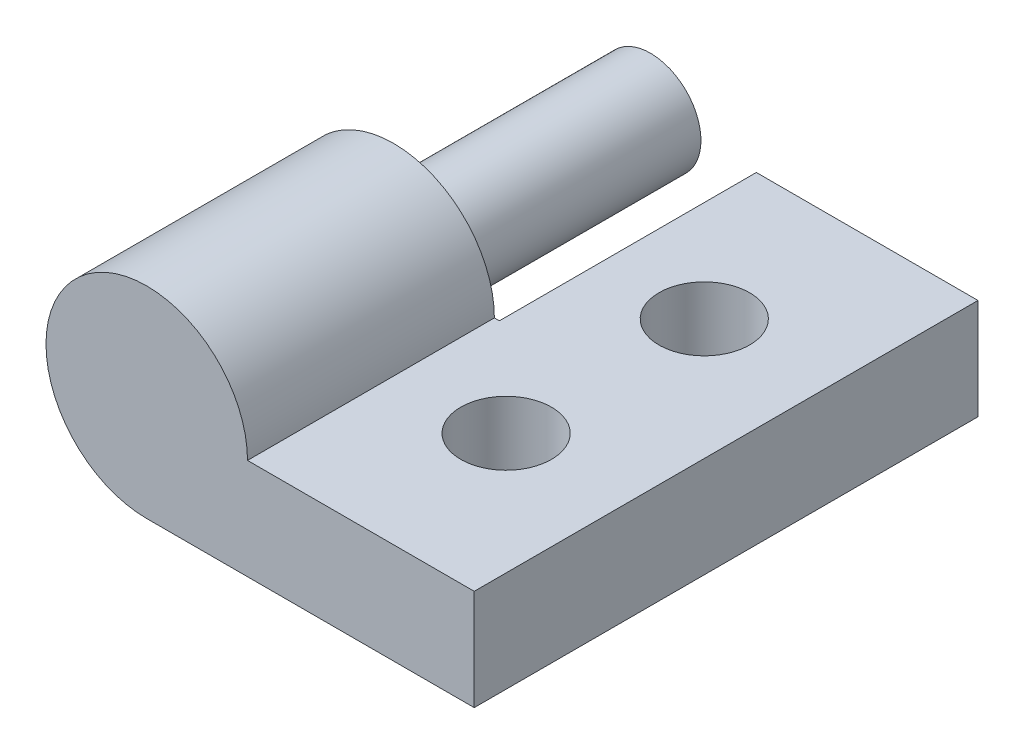
SolidWorks part; units mm, degrees
ref_plane "Front Plane" through (0, 0, 0) normal (0, 0, 1) x (1, 0, 0)
ref_plane "Top Plane" through (0, 0, 0) normal (0, 1, 0) x (1, 0, 0)
ref_plane "Right Plane" through (0, 0, 0) normal (1, 0, 0) x (0, 0, -1)
sketch "Sketch2" plane through (0, 0, 0) normal (0, 0, 1) x (1, 0, 0)
  line L1 (0, 0) -> (-16.51, 0)
  line L2 (0, 0) -> (0, 5.08)
  line L3 (0, 5.08) -> (-11.43, 5.08)
  arc A0 (-11.43, 5.08) -> (-16.51, 0) centre (-16.51, 5.08) ccw
  dimension "D3" = 5.08
  dimension "D1" = 16.51
  dimension "D2" = 5.08
extrude "Boss-Extrude1" add sketch "Sketch2" along normal blind 25.4
sketch "Sketch5" plane through (0, 5.08, 0) normal (0, 1, 0) x (1, 0, 0)
  line L0 (-6.096, -15.4093) -> (-6.096, -9.9907) construction
  line L1 (-6.096, -19.9813) -> (-6.096, -25.4) construction
  line L2 (0, -25.4) -> (-11.43, -25.4) construction
  line L3 (-6.096, -5.4187) -> (-6.096, 0) construction
  line L4 (0, 0) -> (-11.43, 0) construction
  line L5 (-6.096, -7.7047) -> (-16.51, -7.7047) construction
  line L9 (-16.51, -25.4) -> (-16.51, 0) construction
  circle A0 centre (-6.096, -17.6953) radius 2.286
  circle A1 centre (-6.096, -7.7047) radius 2.286
  dimension "D1" = 4.572
  dimension "D2" = 4.572
  dimension "D3" = 10.414
extrude "Cut-Extrude3" cut sketch "Sketch5" against normal blind 12.954
sketch "Sketch8" plane through (0, 0, 0) normal (0, 0, -1) x (-1, 0, 0)
  circle A0 centre (19.3527, 9.2811) radius 0.0075
  circle A1 centre (16.51, 5.08) radius 5.08
  circle A2 centre (16.51, 5.08) radius 5.334
  dimension "D1" = 10.668
extrude "Cut-Extrude5" cut sketch "Sketch8" against normal blind 12.954 contours A2
sketch "Sketch9" plane through (0, 0, 12.954) normal (0, 0, -1) x (-1, 0, 0)
  circle A0 centre (16.51, 5.08) radius 5.08
  circle A1 centre (16.51, 5.08) radius 2.54
  dimension "D1" = 5.08
extrude "Boss-Extrude2" add sketch "Sketch9" along normal blind 12.954 contours A1
sketch "Sketch10" plane through (0, 0, 0) normal (0, 0, -1) x (-1, 0, 0)
  line L2 (11.176, 5.08) -> (11.176, 0)
  line L3 (11.176, 0) -> (14.8836, 0)
  arc A0 (11.176, 5.08) -> (14.8836, 0) centre (16.51, 5.08) ccw construction
  arc A1 (11.176, 5.08) -> (14.8836, 0) centre (16.51, 5.08) ccw
extrude "Cut-Extrude7" cut sketch "Sketch10" against normal up to surface (12.954 mm away) up to face at (-19.05, 5.08, 12.954)
